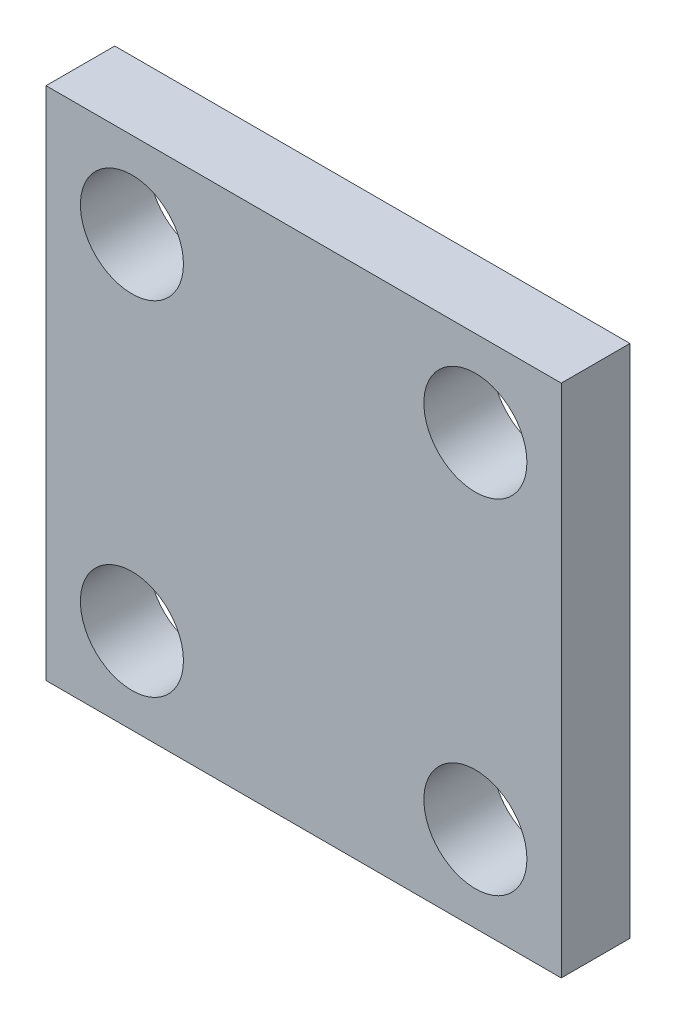
SolidWorks part; units mm, degrees
ref_plane "Plan de face" through (0, 0, 0) normal (0, 0, 1) x (1, 0, 0)
ref_plane "Plan de dessus" through (0, 0, 0) normal (0, 1, 0) x (1, 0, 0)
ref_plane "Plan de droite" through (0, 0, 0) normal (1, 0, 0) x (0, 0, -1)
sketch "Esquisse3" plane through (0, 0, 0) normal (0, 0, 1) x (1, 0, 0)
  line L1 (-30, -30) -> (30, -30)
  line L2 (-30, -30) -> (-30, 30)
  line L3 (-30, 30) -> (30, 30)
  line L4 (30, -30) -> (30, 30)
  line L5 (-30, -30) -> (30, 30) construction
  line L6 (-30, 30) -> (30, -30) construction
  circle A0 centre (-20, 20) radius 6
  circle A1 centre (20, 20) radius 6
  circle A2 centre (-20, -20) radius 6
  circle A3 centre (20, -20) radius 6
  point P0 (0, 0)
  dimension "D4" = 40
  dimension "D3" = 40
  dimension "D1" = 60
  dimension "D2" = 60
  dimension "D5" = 40
  dimension "D6" = 40
extrude "Boss.-Extru.4" add sketch "Esquisse3" along normal blind 8
